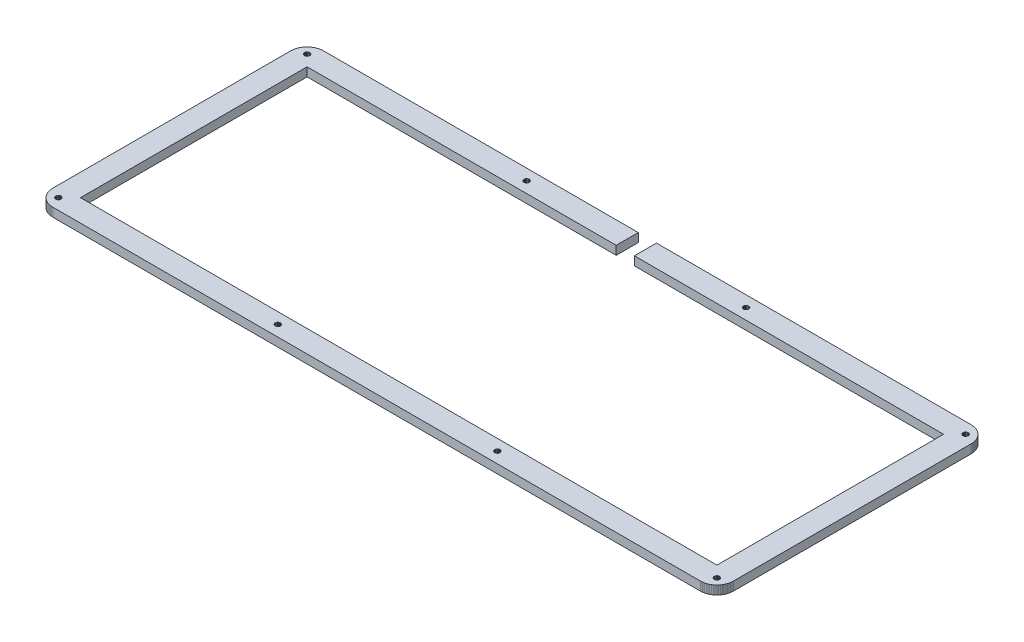
SolidWorks part; units mm, degrees
material "Acrylic (Medium-high impact)"
ref_plane "Front Plane" through (0, 0, 0) normal (0, 0, 1) x (1, 0, 0)
ref_plane "Top Plane" through (0, 0, 0) normal (0, 1, 0) x (1, 0, 0)
ref_plane "Right Plane" through (0, 0, 0) normal (1, 0, 0) x (0, 0, -1)
sketch "Sketch1" plane through (0, 0, 0) normal (0, 1, 0) x (1, 0, 0)
  line L0 (180.976, 147.968) -> (180.976, 135.919)
  line L1 (180.976, 135.919) -> (12.1447, 135.919)
  line L2 (12.1447, 135.919) -> (12.1447, 12.1405)
  line L3 (12.1447, 12.1405) -> (359.759, 12.1405)
  line L4 (359.759, 12.1405) -> (359.759, 135.919)
  line L5 (359.759, 135.919) -> (190.926, 135.919)
  line L6 (190.926, 135.919) -> (190.926, 147.967)
  line L7 (190.926, 147.967) -> (362.807, 147.967)
  line L8 (362.807, 147.967) -> (363.513, 147.941)
  line L9 (363.513, 147.941) -> (364.215, 147.857)
  line L10 (364.215, 147.857) -> (364.91, 147.719)
  line L11 (364.91, 147.719) -> (365.591, 147.527)
  line L12 (365.591, 147.527) -> (366.254, 147.282)
  line L13 (366.254, 147.282) -> (366.896, 146.987)
  line L14 (366.896, 146.987) -> (367.51, 146.641)
  line L15 (367.51, 146.641) -> (368.099, 146.25)
  line L16 (368.099, 146.25) -> (368.653, 145.812)
  line L17 (368.653, 145.812) -> (369.171, 145.331)
  line L18 (369.171, 145.331) -> (369.651, 144.812)
  line L19 (369.651, 144.812) -> (370.089, 144.259)
  line L20 (370.089, 144.259) -> (370.48, 143.67)
  line L21 (370.48, 143.67) -> (370.826, 143.053)
  line L22 (370.826, 143.053) -> (371.122, 142.412)
  line L23 (371.122, 142.412) -> (371.369, 141.749)
  line L24 (371.369, 141.749) -> (371.56, 141.07)
  line L25 (371.56, 141.07) -> (371.697, 140.375)
  line L26 (371.697, 140.375) -> (371.778, 139.674)
  line L27 (371.778, 139.674) -> (371.807, 138.967)
  line L28 (371.807, 138.967) -> (371.807, 9.0909)
  line L29 (371.807, 9.0909) -> (371.778, 8.3854)
  line L30 (371.778, 8.3854) -> (371.697, 7.684)
  line L31 (371.697, 7.684) -> (371.56, 6.9908)
  line L32 (371.56, 6.9908) -> (371.369, 6.31)
  line L33 (371.369, 6.31) -> (371.122, 5.6472)
  line L34 (371.122, 5.6472) -> (370.826, 5.0064)
  line L35 (370.826, 5.0064) -> (370.48, 4.3891)
  line L36 (370.48, 4.3891) -> (370.089, 3.8006)
  line L37 (370.089, 3.8006) -> (369.651, 3.2467)
  line L38 (369.651, 3.2467) -> (369.171, 2.7285)
  line L39 (369.171, 2.7285) -> (368.653, 2.2476)
  line L40 (368.653, 2.2476) -> (368.099, 1.8107)
  line L41 (368.099, 1.8107) -> (367.51, 1.418)
  line L42 (367.51, 1.418) -> (366.896, 1.0721)
  line L43 (366.896, 1.0721) -> (366.254, 0.7772)
  line L44 (366.254, 0.7772) -> (365.591, 0.5319)
  line L45 (365.591, 0.5319) -> (364.91, 0.3404)
  line L46 (364.91, 0.3404) -> (364.215, 0.2026)
  line L47 (364.215, 0.2026) -> (363.513, 0.1185)
  line L48 (363.513, 0.1185) -> (362.807, 0.091)
  line L49 (362.807, 0.091) -> (9.0951, 0.091)
  line L50 (9.0951, 0.091) -> (8.3881, 0.1185)
  line L51 (8.3881, 0.1185) -> (7.6867, 0.2026)
  line L52 (7.6867, 0.2026) -> (6.9922, 0.3404)
  line L53 (6.9922, 0.3404) -> (6.3128, 0.5319)
  line L54 (6.3128, 0.5319) -> (5.6499, 0.7772)
  line L55 (5.6499, 0.7772) -> (5.0092, 1.0721)
  line L56 (5.0092, 1.0721) -> (4.3918, 1.418)
  line L57 (4.3918, 1.418) -> (3.8034, 1.8107)
  line L58 (3.8034, 1.8107) -> (3.2494, 2.2476)
  line L59 (3.2494, 2.2476) -> (2.7313, 2.7285)
  line L60 (2.7313, 2.7285) -> (2.2503, 3.2467)
  line L61 (2.2503, 3.2467) -> (1.8121, 3.8006)
  line L62 (1.8121, 3.8006) -> (1.4208, 4.3891)
  line L63 (1.4208, 4.3891) -> (1.0749, 5.0064)
  line L64 (1.0749, 5.0064) -> (0.78, 5.6472)
  line L65 (0.78, 5.6472) -> (0.5347, 6.31)
  line L66 (0.5347, 6.31) -> (0.3431, 6.9908)
  line L67 (0.3431, 6.9908) -> (0.2053, 7.684)
  line L68 (0.2053, 7.684) -> (0.1213, 8.3854)
  line L69 (0.1213, 8.3854) -> (0.0937, 9.0923)
  line L70 (0.0937, 9.0923) -> (0.0951, 138.967)
  line L71 (0.0951, 138.967) -> (0.1213, 139.674)
  line L72 (0.1213, 139.674) -> (0.2053, 140.375)
  line L73 (0.2053, 140.375) -> (0.3431, 141.07)
  line L74 (0.3431, 141.07) -> (0.5347, 141.749)
  line L75 (0.5347, 141.749) -> (0.78, 142.412)
  line L76 (0.78, 142.412) -> (1.0749, 143.053)
  line L77 (1.0749, 143.053) -> (1.4208, 143.67)
  line L78 (1.4208, 143.67) -> (1.8121, 144.259)
  line L79 (1.8121, 144.259) -> (2.2503, 144.812)
  line L80 (2.2503, 144.812) -> (2.7313, 145.331)
  line L81 (2.7313, 145.331) -> (3.2494, 145.812)
  line L82 (3.2494, 145.812) -> (3.8034, 146.25)
  line L83 (3.8034, 146.25) -> (4.3918, 146.641)
  line L84 (4.3918, 146.641) -> (5.0092, 146.987)
  line L85 (5.0092, 146.987) -> (5.6499, 147.282)
  line L86 (5.6499, 147.282) -> (6.3128, 147.527)
  line L87 (6.3128, 147.527) -> (6.9922, 147.719)
  line L88 (6.9922, 147.719) -> (7.6867, 147.857)
  line L89 (7.6867, 147.857) -> (8.3881, 147.941)
  line L90 (8.3881, 147.941) -> (9.0951, 147.968)
  line L91 (9.0951, 147.968) -> (180.976, 147.968)
  line L92 (365.326, 7.5186) -> (364.917, 7.3119)
  line L93 (364.917, 7.3119) -> (364.589, 6.9825)
  line L94 (364.589, 6.9825) -> (364.381, 6.5719)
  line L95 (364.381, 6.5719) -> (364.307, 6.1157)
  line L96 (364.307, 6.1157) -> (364.381, 5.661)
  line L97 (364.381, 5.661) -> (364.589, 5.2503)
  line L98 (364.589, 5.2503) -> (364.917, 4.9237)
  line L99 (364.917, 4.9237) -> (365.326, 4.7143)
  line L100 (365.326, 4.7143) -> (365.781, 4.6413)
  line L101 (365.781, 4.6413) -> (366.24, 4.7143)
  line L102 (366.24, 4.7143) -> (366.649, 4.9237)
  line L103 (366.649, 4.9237) -> (366.977, 5.2503)
  line L104 (366.977, 5.2503) -> (367.185, 5.661)
  line L105 (367.185, 5.661) -> (367.259, 6.1157)
  line L106 (367.259, 6.1157) -> (367.185, 6.5719)
  line L107 (367.185, 6.5719) -> (366.977, 6.9825)
  line L108 (366.977, 6.9825) -> (366.649, 7.3119)
  line L109 (366.649, 7.3119) -> (366.24, 7.5186)
  line L110 (366.24, 7.5186) -> (365.781, 7.5916)
  line L111 (365.781, 7.5916) -> (365.326, 7.5186)
  line L112 (245.438, 7.5186) -> (245.027, 7.3119)
  line L113 (245.027, 7.3119) -> (244.703, 6.9825)
  line L114 (244.703, 6.9825) -> (244.492, 6.5719)
  line L115 (244.492, 6.5719) -> (244.42, 6.1157)
  line L116 (244.42, 6.1157) -> (244.492, 5.661)
  line L117 (244.492, 5.661) -> (244.703, 5.2503)
  line L118 (244.703, 5.2503) -> (245.027, 4.9237)
  line L119 (245.027, 4.9237) -> (245.438, 4.7143)
  line L120 (245.438, 4.7143) -> (245.894, 4.6413)
  line L121 (245.894, 4.6413) -> (246.35, 4.7143)
  line L122 (246.35, 4.7143) -> (246.761, 4.9237)
  line L123 (246.761, 4.9237) -> (247.088, 5.2503)
  line L124 (247.088, 5.2503) -> (247.297, 5.661)
  line L125 (247.297, 5.661) -> (247.37, 6.1157)
  line L126 (247.37, 6.1157) -> (247.297, 6.5719)
  line L127 (247.297, 6.5719) -> (247.088, 6.9825)
  line L128 (247.088, 6.9825) -> (246.761, 7.3119)
  line L129 (246.761, 7.3119) -> (246.35, 7.5186)
  line L130 (246.35, 7.5186) -> (245.894, 7.5916)
  line L131 (245.894, 7.5916) -> (245.438, 7.5186)
  line L132 (125.552, 7.5186) -> (125.138, 7.3119)
  line L133 (125.138, 7.3119) -> (124.815, 6.9825)
  line L134 (124.815, 6.9825) -> (124.604, 6.5719)
  line L135 (124.604, 6.5719) -> (124.532, 6.1157)
  line L136 (124.532, 6.1157) -> (124.604, 5.661)
  line L137 (124.604, 5.661) -> (124.815, 5.2503)
  line L138 (124.815, 5.2503) -> (125.138, 4.9237)
  line L139 (125.138, 4.9237) -> (125.552, 4.7143)
  line L140 (125.552, 4.7143) -> (126.007, 4.6413)
  line L141 (126.007, 4.6413) -> (126.463, 4.7143)
  line L142 (126.463, 4.7143) -> (126.873, 4.9237)
  line L143 (126.873, 4.9237) -> (127.201, 5.2503)
  line L144 (127.201, 5.2503) -> (127.409, 5.661)
  line L145 (127.409, 5.661) -> (127.482, 6.1157)
  line L146 (127.482, 6.1157) -> (127.409, 6.5719)
  line L147 (127.409, 6.5719) -> (127.201, 6.9825)
  line L148 (127.201, 6.9825) -> (126.873, 7.3119)
  line L149 (126.873, 7.3119) -> (126.463, 7.5186)
  line L150 (126.463, 7.5186) -> (126.007, 7.5916)
  line L151 (126.007, 7.5916) -> (125.552, 7.5186)
  line L152 (5.6637, 7.5186) -> (5.2531, 7.3119)
  line L153 (5.2531, 7.3119) -> (4.9251, 6.9825)
  line L154 (4.9251, 6.9825) -> (4.717, 6.5719)
  line L155 (4.717, 6.5719) -> (4.644, 6.1157)
  line L156 (4.644, 6.1157) -> (4.717, 5.661)
  line L157 (4.717, 5.661) -> (4.9251, 5.2503)
  line L158 (4.9251, 5.2503) -> (5.2531, 4.9237)
  line L159 (5.2531, 4.9237) -> (5.6637, 4.7143)
  line L160 (5.6637, 4.7143) -> (6.1185, 4.6413)
  line L161 (6.1185, 4.6413) -> (6.5746, 4.7143)
  line L162 (6.5746, 4.7143) -> (6.9853, 4.9237)
  line L163 (6.9853, 4.9237) -> (7.3133, 5.2503)
  line L164 (7.3133, 5.2503) -> (7.5213, 5.661)
  line L165 (7.5213, 5.661) -> (7.5944, 6.1157)
  line L166 (7.5944, 6.1157) -> (7.5213, 6.5719)
  line L167 (7.5213, 6.5719) -> (7.3133, 6.9825)
  line L168 (7.3133, 6.9825) -> (6.9853, 7.3119)
  line L169 (6.9853, 7.3119) -> (6.5746, 7.5186)
  line L170 (6.5746, 7.5186) -> (6.1185, 7.5916)
  line L171 (6.1185, 7.5916) -> (5.6637, 7.5186)
  line L172 (125.552, 143.345) -> (125.138, 143.137)
  line L173 (125.138, 143.137) -> (124.815, 142.809)
  line L174 (124.815, 142.809) -> (124.604, 142.398)
  line L175 (124.604, 142.398) -> (124.532, 141.942)
  line L176 (124.532, 141.942) -> (124.604, 141.487)
  line L177 (124.604, 141.487) -> (124.815, 141.077)
  line L178 (124.815, 141.077) -> (125.138, 140.75)
  line L179 (125.138, 140.75) -> (125.552, 140.541)
  line L180 (125.552, 140.541) -> (126.007, 140.468)
  line L181 (126.007, 140.468) -> (126.463, 140.541)
  line L182 (126.463, 140.541) -> (126.873, 140.75)
  line L183 (126.873, 140.75) -> (127.201, 141.077)
  line L184 (127.201, 141.077) -> (127.409, 141.487)
  line L185 (127.409, 141.487) -> (127.482, 141.942)
  line L186 (127.482, 141.942) -> (127.409, 142.398)
  line L187 (127.409, 142.398) -> (127.201, 142.809)
  line L188 (127.201, 142.809) -> (126.873, 143.137)
  line L189 (126.873, 143.137) -> (126.463, 143.345)
  line L190 (126.463, 143.345) -> (126.007, 143.417)
  line L191 (126.007, 143.417) -> (125.552, 143.345)
  line L192 (245.438, 143.345) -> (245.027, 143.137)
  line L193 (245.027, 143.137) -> (244.703, 142.809)
  line L194 (244.703, 142.809) -> (244.492, 142.398)
  line L195 (244.492, 142.398) -> (244.42, 141.942)
  line L196 (244.42, 141.942) -> (244.492, 141.487)
  line L197 (244.492, 141.487) -> (244.703, 141.077)
  line L198 (244.703, 141.077) -> (245.027, 140.75)
  line L199 (245.027, 140.75) -> (245.438, 140.541)
  line L200 (245.438, 140.541) -> (245.894, 140.468)
  line L201 (245.894, 140.468) -> (246.35, 140.541)
  line L202 (246.35, 140.541) -> (246.761, 140.75)
  line L203 (246.761, 140.75) -> (247.088, 141.077)
  line L204 (247.088, 141.077) -> (247.297, 141.487)
  line L205 (247.297, 141.487) -> (247.37, 141.942)
  line L206 (247.37, 141.942) -> (247.297, 142.398)
  line L207 (247.297, 142.398) -> (247.088, 142.809)
  line L208 (247.088, 142.809) -> (246.761, 143.137)
  line L209 (246.761, 143.137) -> (246.35, 143.345)
  line L210 (246.35, 143.345) -> (245.894, 143.417)
  line L211 (245.894, 143.417) -> (245.438, 143.345)
  line L212 (365.326, 143.345) -> (364.917, 143.137)
  line L213 (364.917, 143.137) -> (364.589, 142.809)
  line L214 (364.589, 142.809) -> (364.381, 142.398)
  line L215 (364.381, 142.398) -> (364.307, 141.942)
  line L216 (364.307, 141.942) -> (364.381, 141.487)
  line L217 (364.381, 141.487) -> (364.589, 141.077)
  line L218 (364.589, 141.077) -> (364.917, 140.75)
  line L219 (364.917, 140.75) -> (365.326, 140.541)
  line L220 (365.326, 140.541) -> (365.781, 140.468)
  line L221 (365.781, 140.468) -> (366.24, 140.541)
  line L222 (366.24, 140.541) -> (366.649, 140.75)
  line L223 (366.649, 140.75) -> (366.977, 141.077)
  line L224 (366.977, 141.077) -> (367.185, 141.487)
  line L225 (367.185, 141.487) -> (367.259, 141.942)
  line L226 (367.259, 141.942) -> (367.185, 142.398)
  line L227 (367.185, 142.398) -> (366.977, 142.809)
  line L228 (366.977, 142.809) -> (366.649, 143.137)
  line L229 (366.649, 143.137) -> (366.24, 143.345)
  line L230 (366.24, 143.345) -> (365.781, 143.417)
  line L231 (365.781, 143.417) -> (365.326, 143.345)
  line L232 (5.6637, 143.345) -> (5.2531, 143.137)
  line L233 (5.2531, 143.137) -> (4.9251, 142.809)
  line L234 (4.9251, 142.809) -> (4.717, 142.398)
  line L235 (4.717, 142.398) -> (4.644, 141.942)
  line L236 (4.644, 141.942) -> (4.717, 141.487)
  line L237 (4.717, 141.487) -> (4.9251, 141.077)
  line L238 (4.9251, 141.077) -> (5.2531, 140.75)
  line L239 (5.2531, 140.75) -> (5.6637, 140.541)
  line L240 (5.6637, 140.541) -> (6.1185, 140.468)
  line L241 (6.1185, 140.468) -> (6.5746, 140.541)
  line L242 (6.5746, 140.541) -> (6.9853, 140.75)
  line L243 (6.9853, 140.75) -> (7.3133, 141.077)
  line L244 (7.3133, 141.077) -> (7.5213, 141.487)
  line L245 (7.5213, 141.487) -> (7.5944, 141.942)
  line L246 (7.5944, 141.942) -> (7.5213, 142.398)
  line L247 (7.5213, 142.398) -> (7.3133, 142.809)
  line L248 (7.3133, 142.809) -> (6.9853, 143.137)
  line L249 (6.9853, 143.137) -> (6.5746, 143.345)
  line L250 (6.5746, 143.345) -> (6.1185, 143.417)
  line L251 (6.1185, 143.417) -> (5.6637, 143.345)
extrude "Boss-Extrude1" add sketch "Sketch1" along normal blind 4.7625
